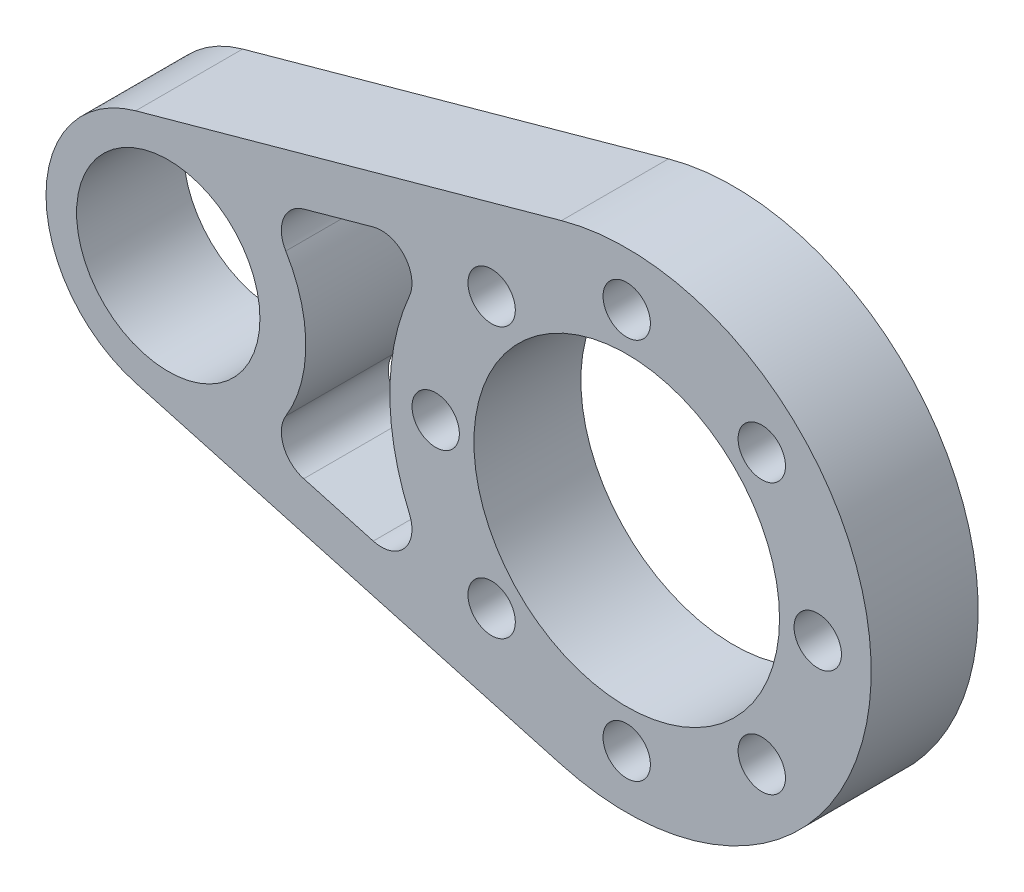
SolidWorks part; units mm, degrees
material "Thornel Mat VMA"
ref_plane "前视基准面" through (0, 0, 0) normal (0, 0, 1) x (1, 0, 0)
ref_plane "上视基准面" through (0, 0, 0) normal (0, 1, 0) x (1, 0, 0)
ref_plane "右视基准面" through (0, 0, 0) normal (1, 0, 0) x (0, 0, -1)
sketch "草图1" plane through (0, 0, 0) normal (0, 0, 1) x (1, 0, 0)
  line L0 (0, 0) -> (30, 0) construction
  line L1 (0, 16) -> (30, 16) construction
  line L2 (0, -16) -> (30, -16) construction
  line L3 (25.7333, -15.4206) -> (-2.1333, -7.7103)
  line L4 (25.7333, 15.4206) -> (-2.1333, 7.7103)
  line L5 (30, 0) -> (30, -12.5) construction
  line L6 (26.5333, -12.5293) -> (-1.3333, -4.8189) construction
  line L7 (26.5333, 12.5293) -> (-1.3333, 4.8189) construction
  line L8 (5.879, -6.8145) -> (18.398, -10.2783)
  line L10 (18.398, 10.2783) -> (5.879, 6.8145)
  arc A0 (0, 16) -> (0, -16) centre (0, 0) ccw construction
  arc A1 (30, -16) -> (30, 16) centre (30, 0) ccw construction
  circle A2 centre (0, 0) radius 6
  circle A3 centre (30, 0) radius 10
  arc A4 (-2.1333, 7.7103) -> (-2.1333, -7.7103) centre (0, 0) ccw
  arc A5 (25.7333, -15.4206) -> (25.7333, 15.4206) centre (30, 0) ccw
  circle A6 centre (30, 0) radius 12.5 construction
  circle A7 centre (30, -12.5) radius 1.55
  circle A8 centre (21.1612, -8.8388) radius 1.55
  circle A9 centre (17.5, 0) radius 1.55
  circle A10 centre (21.1612, 8.8388) radius 1.55
  circle A11 centre (30, 12.5) radius 1.55
  circle A12 centre (38.8388, 8.8388) radius 1.55
  circle A13 centre (42.5, 0) radius 1.55
  circle A14 centre (38.8388, -8.8388) radius 1.55
  circle A15 centre (30, 0) radius 15.5 construction
  circle A16 centre (0, 0) radius 9 construction
  arc A18 (5.879, -6.8145) -> (5.879, 6.8145) centre (0, 0) ccw
  arc A19 (18.398, -10.2783) -> (18.398, 10.2783) centre (30, 0) cw
  point P3 (15, 0)
  dimension "D1" = 12
  dimension "D3" = 20
  dimension "D4" = 16
  dimension "D5" = 16
  dimension "D6" = 25
  dimension "D7" = 8
  dimension "D9" = 3.1
  dimension "D2" = 30
  dimension "D8" = 12.5
  dimension "D10" = 3
  dimension "D11" = 3
  dimension "D12" = 3
extrude "凸台-拉伸1" add sketch "草图1" along normal blind 7
fillet "圆角1" radius 2 4 edges at (18.398, 10.2783, 3.5) (5.879, 6.8145, 3.5) (5.879, -6.8145, 3.5) (18.398, -10.2783, 3.5)
